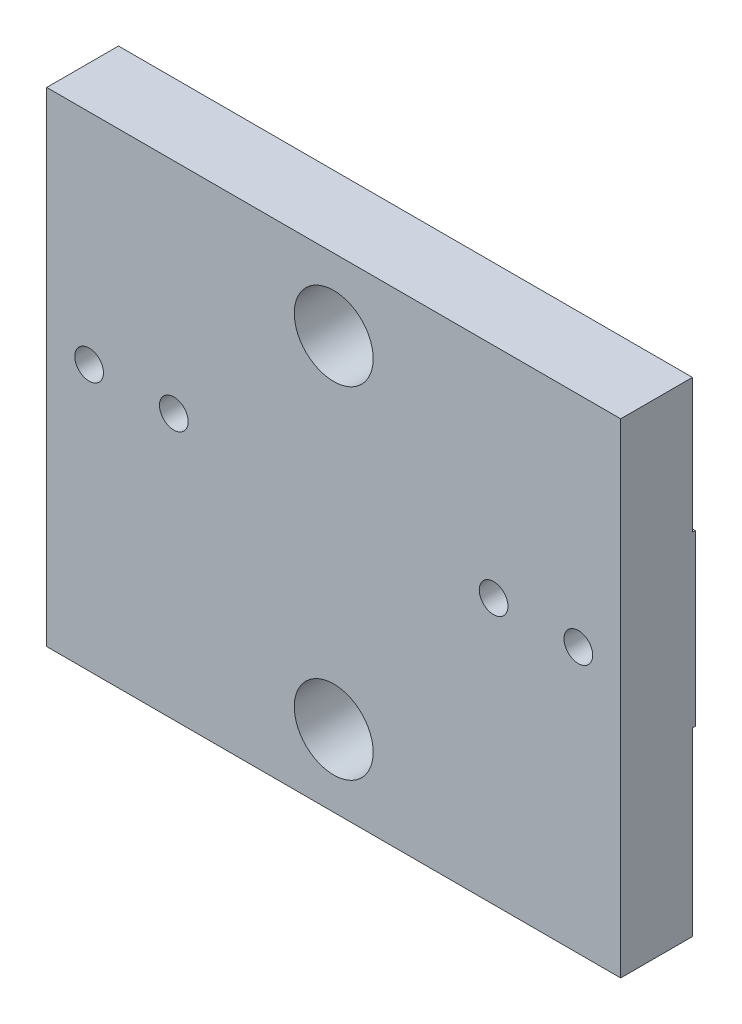
SolidWorks part; units mm, degrees
material "Silicon"
ref_plane "Front Plane" through (0, 0, 0) normal (0, 0, 1) x (1, 0, 0)
ref_plane "Top Plane" through (0, 0, 0) normal (0, 1, 0) x (1, 0, 0)
ref_plane "Right Plane" through (0, 0, 0) normal (1, 0, 0) x (0, 0, -1)
sketch "Sketch1" plane through (0, 0, 0) normal (0, 0, 1) x (1, 0, 0)
  line L0 (-10.16, -8.5725) -> (10.16, -8.5725)
  line L1 (-10.16, -8.5725) -> (-10.16, 8.5725)
  line L2 (10.16, -8.5725) -> (10.16, 8.5725)
  line L3 (-10.16, 8.5725) -> (10.16, 8.5725)
  line L4 (-10.16, 3.8255) -> (-7.16, 3.8255) construction
  line L5 (-7.16, 3.8255) -> (-7.16, -2.1745) construction
  line L6 (0, 8.5725) -> (0, -8.5725) construction
  line L7 (-7.16, -2.1745) -> (-10.16, -2.1745) construction
  line L8 (7.16, -2.1745) -> (10.16, -2.1745) construction
  line L9 (7.16, 3.8255) -> (7.16, -2.1745) construction
  line L10 (10.16, 3.8255) -> (7.16, 3.8255) construction
  circle A0 centre (0, -6.0325) radius 1.397
  circle A1 centre (0, 6.0325) radius 1.397
  circle A2 centre (-8.66, 0.8255) radius 0.508
  circle A3 centre (8.66, 0.8255) radius 0.508
  circle A4 centre (-5.66, 0.8255) radius 0.508
  circle A5 centre (5.66, 0.8255) radius 0.508
  point P1 (0, 0)
  dimension "D4" = 2.794
  dimension "D6" = 2.794
  dimension "D7" = 1.016
  dimension "D9" = 1.5
  dimension "D13" = 1.016
  dimension "D1" = 17.145
  dimension "D2" = 20.32
  dimension "D3" = 2.54
  dimension "D5" = 12.065
  dimension "D8" = 9.398
  dimension "D10" = 3
  dimension "D11" = 3
  dimension "D12" = 1.5
  dimension "D14" = 1.5
extrude "Board" add sketch "Sketch1" along normal blind 2.54
sketch "Sketch2" plane through (0, 0, 0) normal (0, 0, 1) x (1, 0, 0)
  line L0 (10.16, 3.8255) -> (7.16, 3.8255) construction
  line L1 (7.16, 3.8255) -> (7.16, -2.1745) construction
  line L2 (7.16, -2.1745) -> (10.16, -2.1745) construction
  line L3 (10.16, -8.5725) -> (10.16, 8.5725) construction
  line L4 (-7.16, 3.8255) -> (-7.16, -2.1745) construction
  line L5 (-10.16, 3.8255) -> (-7.16, 3.8255) construction
  line L6 (-7.16, -2.1745) -> (-10.16, -2.1745) construction
  line L7 (-10.16, -8.5725) -> (-10.16, 8.5725) construction
  line L8 (10.16, 3.8255) -> (7.16, 3.8255)
  line L9 (7.16, 3.8255) -> (7.16, -2.1745)
  line L10 (7.16, -2.1745) -> (10.16, -2.1745)
  line L11 (10.16, -8.5725) -> (10.16, 8.5725)
  line L12 (-7.16, 3.8255) -> (-7.16, -2.1745)
  line L13 (-10.16, 3.8255) -> (-7.16, 3.8255)
  line L14 (-7.16, -2.1745) -> (-10.16, -2.1745)
  line L15 (-10.16, -8.5725) -> (-10.16, 8.5725)
  line L16 (10.16, -7.9295) -> (-10.16, -7.9295) construction
  line L17 (10.16, -8.5725) -> (10.16, 8.5725) construction
  line L18 (7.91, 4.0379) -> (7.91, 5.4274) construction
  line L19 (-8.66, 4.5255) -> (-7.16, 4.5255)
  line L20 (-8.66, 4.5255) -> (-8.66, 4.9255)
  line L21 (-8.66, 4.9255) -> (-7.16, 4.9255)
  line L22 (-7.16, 4.5255) -> (-7.16, 4.9255)
  line L23 (7.71, 4.0379) -> (8.11, 4.0379)
  line L24 (7.71, 4.0379) -> (7.71, 5.4274)
  line L25 (7.71, 5.4274) -> (8.11, 5.4274)
  line L26 (8.11, 4.0379) -> (8.11, 5.4274)
  line L27 (7.16, 4.5255) -> (8.66, 4.5255)
  line L28 (7.16, 4.5255) -> (7.16, 4.9255)
  line L29 (7.16, 4.9255) -> (8.66, 4.9255)
  line L30 (8.66, 4.5255) -> (8.66, 4.9255)
  circle A0 centre (8.66, 0.8255) radius 0.508 construction
  circle A1 centre (-8.66, 0.8255) radius 0.508 construction
  circle A2 centre (8.66, 0.8255) radius 0.508
  circle A3 centre (-8.66, 0.8255) radius 0.508
  circle A5 centre (0, -6.0325) radius 1.397 construction
  circle A6 centre (0, -6.0325) radius 1.397
  circle A9 centre (5.66, 0.8255) radius 1.008
  circle A10 centre (5.66, 0.8255) radius 1.008
  circle A11 centre (5.66, 0.8255) radius 0.508 construction
  circle A12 centre (-5.66, 0.8255) radius 1.008
  circle A13 centre (-5.66, 0.8255) radius 1.008
  circle A14 centre (-5.66, 0.8255) radius 0.508 construction
  circle A15 centre (5.66, 0.8255) radius 0.508
  circle A16 centre (-5.66, 0.8255) radius 0.508
  point P19 (0, -7.9295)
  point P48 (-8.66, 3.8255)
  point P49 (8.66, 3.8255)
  point P52 (7.91, 4.5255)
  dimension "D4" = 2.794
  dimension "D3" = 1.897
  dimension "D5" = 0.4
  dimension "D6" = 0.7
  dimension "D7" = 0.4
  dimension "D8" = 0.7
  dimension "D9" = 0.4
  dimension "D1" = 0.5
  dimension "D2" = 0.5
extrude "Solder Pads" add sketch "Sketch2" against normal blind 0.1 contours L10 L11 L8 L9 A2 | L15 L14 L12 L13 A3 | A10 A15 | A13 A16 | L28 L29 L30 L27 | L24 L25 L26 L23 | L19 L22 L21 L20
equation "\"D3@Sketch2\"=\"D4@Sketch2\"/2 + .5mm"
